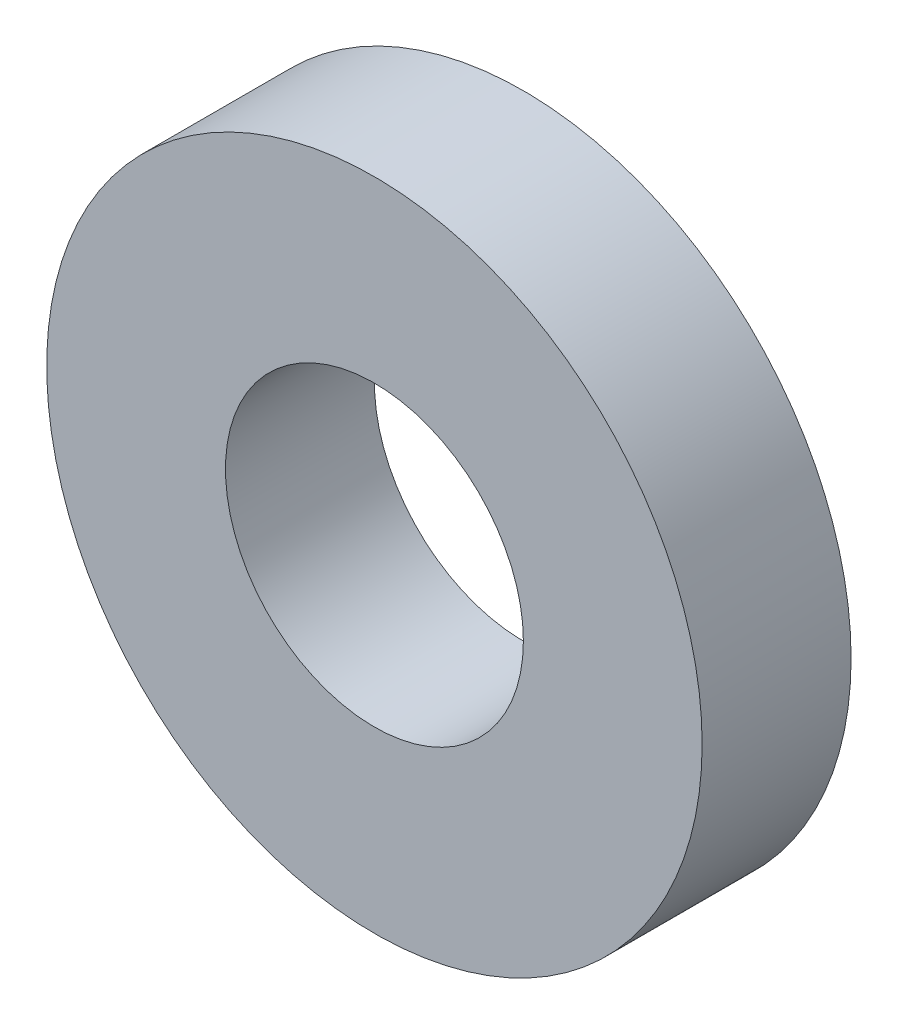
SolidWorks part; units mm, degrees
ref_plane "Front Plane" through (0, 0, 0) normal (0, 0, 1) x (1, 0, 0)
ref_plane "Top Plane" through (0, 0, 0) normal (0, 1, 0) x (1, 0, 0)
ref_plane "Right Plane" through (0, 0, 0) normal (1, 0, 0) x (0, 0, -1)
sketch "Sketch1" plane through (0, 0, 0) normal (0, 0, 1) x (1, 0, 0)
  circle A0 centre (0, 0) radius 6
  circle A1 centre (0, 0) radius 13.2
extrude "Boss-Extrude1" add sketch "Sketch1" along normal blind 6
